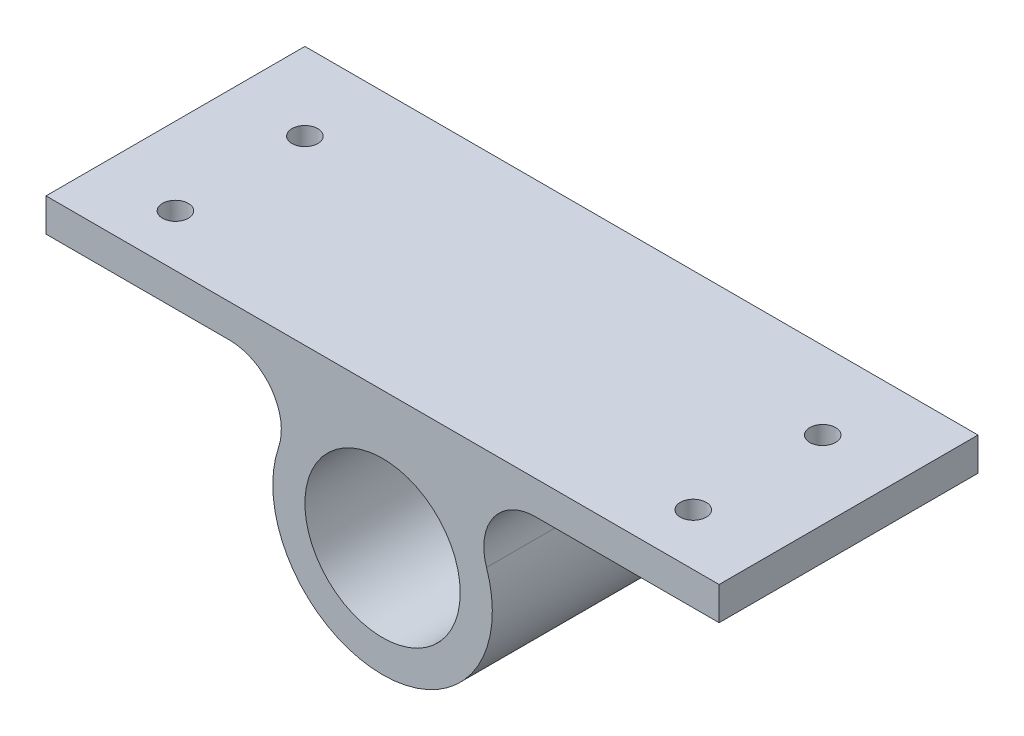
SolidWorks part; units mm, degrees
ref_plane "Front Plane" through (0, 0, 0) normal (0, 0, 1) x (1, 0, 0)
ref_plane "Top Plane" through (0, 0, 0) normal (0, 1, 0) x (1, 0, 0)
ref_plane "Right Plane" through (0, 0, 0) normal (1, 0, 0) x (0, 0, -1)
sketch "Sketch1" plane through (0, 0, 0) normal (0, 1, 0) x (1, 0, 0)
  line L1 (-325, -125) -> (325, -125)
  line L2 (-325, -125) -> (-325, 125)
  line L3 (-325, 125) -> (325, 125)
  line L4 (325, -125) -> (325, 125)
  line L5 (-237.5, 50) -> (-250, 50)
  circle A0 centre (-250, 50) radius 12.5
  circle A1 centre (250, 50) radius 12.5
  circle A2 centre (250, -75) radius 12.5
  circle A3 centre (-250, -75) radius 12.5
  point P0 (0, 0)
  dimension "D5" = 25
  dimension "D1" = 250
  dimension "D2" = 650
  dimension "D6" = 2
  dimension "D7" = 2
extrude "Boss-Extrude1" add sketch "Sketch1" against normal mid plane 238 contours L1 L4 L3 L2 A3 A2 A1 A0
sketch "Sketch2" plane through (0, 0, 125) normal (0, 0, 1) x (1, 0, 0)
  line L0 (-325, 119) -> (325, 119) construction
  line L1 (-325, 119) -> (325, 119)
  line L2 (-325, 87) -> (-35.1568, 87)
  line L3 (-325, 119) -> (-325, 87)
  line L4 (325, 119) -> (325, 87)
  line L5 (35.1568, 87) -> (325, 87)
  line L6 (-325, 87) -> (325, 87) construction
  line L7 (-325, 87) -> (-325, -119)
  line L9 (325, 87) -> (325, -119)
  line L10 (325, -119) -> (-325, -119)
  arc A0 (-35.1568, 87) -> (35.1568, 87) centre (0, -13) ccw
  circle A1 centre (0, -13) radius 75
  line M4 (-325, 119) -> (-325, -119)
  line M5 (-325, -119) -> (325, -119)
  line M6 (325, -119) -> (325, 119)
  dimension "D2" = 106
  dimension "D3" = 75
  dimension "D1" = 32
extrude "Cut-Extrude1" cut sketch "Sketch2" against normal blind 267 contours A0 L2 M4 M5 | A0 L10 L5 M6 | A1
fillet "Fillet1" radius 50 2 edges at (35.1568, 87, 0) (-35.1568, 87, 0)
